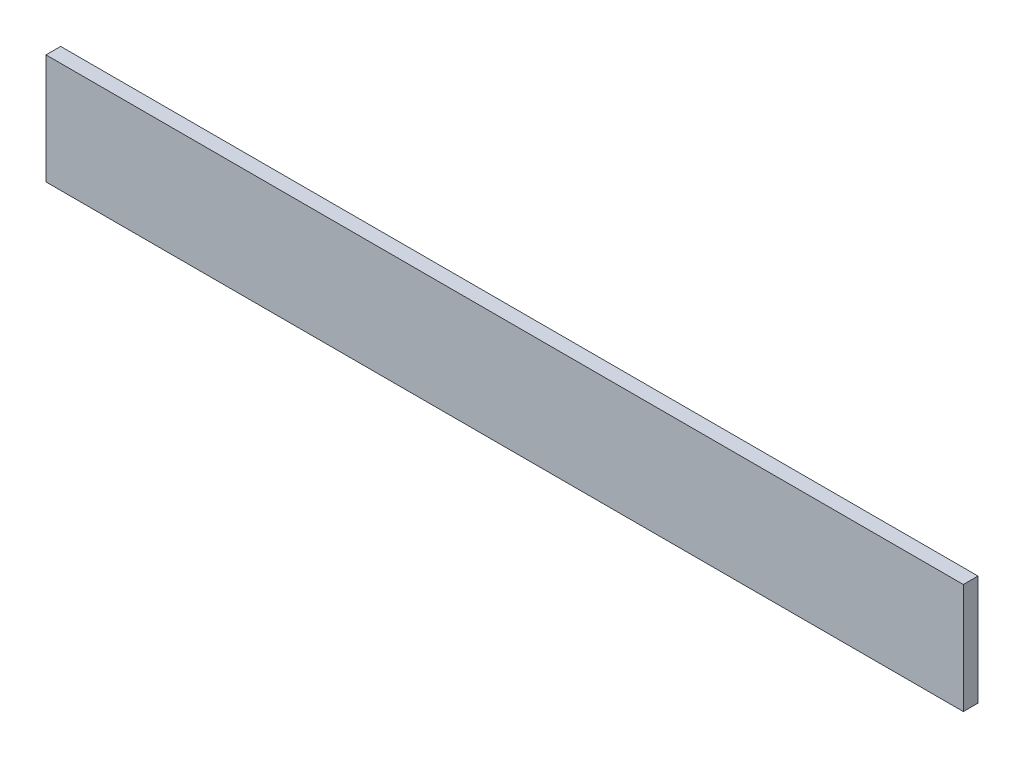
SolidWorks part; units mm, degrees
ref_plane "Front Plane" through (0, 0, 0) normal (0, 0, 1) x (1, 0, 0)
ref_plane "Top Plane" through (0, 0, 0) normal (0, 1, 0) x (1, 0, 0)
ref_plane "Right Plane" through (0, 0, 0) normal (1, 0, 0) x (0, 0, -1)
sketch "Sketch1" plane through (0, 0, 0) normal (0, 0, 1) x (1, 0, 0)
  line L1 (-250, -30) -> (250, -30)
  line L2 (-250, -30) -> (-250, 30)
  line L3 (-250, 30) -> (250, 30)
  line L4 (250, -30) -> (250, 30)
  line L5 (-250, -30) -> (250, 30) construction
  line L6 (-250, 30) -> (250, -30) construction
  point P0 (0, 0)
  dimension "D1" = 500
  dimension "D2" = 60
extrude "Boss-Extrude1" add sketch "Sketch1" along normal mid plane 8
